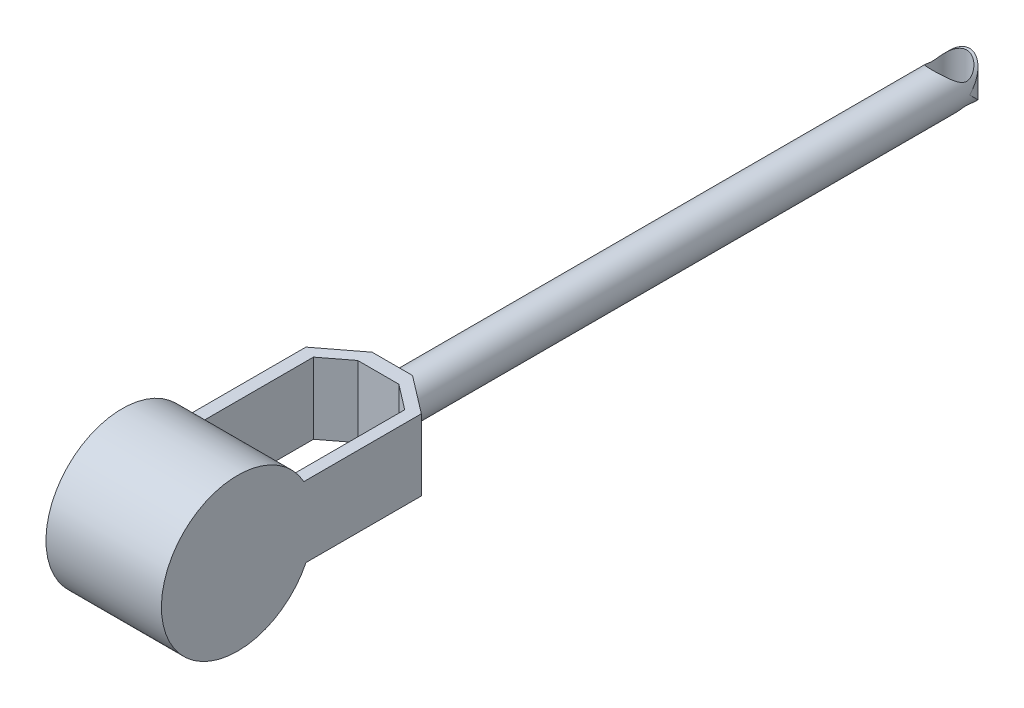
SolidWorks part; units mm, degrees
ref_plane "Front Plane" through (0, 0, 0) normal (0, 0, 1) x (1, 0, 0)
ref_plane "Top Plane" through (0, 0, 0) normal (0, 1, 0) x (1, 0, 0)
ref_plane "Right Plane" through (0, 0, 0) normal (1, 0, 0) x (0, 0, -1)
sketch "Sketch1" plane through (0, 0, 0) normal (0, 0, 1) x (1, 0, 0)
  circle A0 centre (0, 0) radius 35
  dimension "D1" = 70
extrude "Boss-Extrude1" add sketch "Sketch1" along normal blind 1000
sketch "Sketch21" plane through (0, 0, 0) normal (0, 1, 0) x (1, 0, 0)
  line L0 (35, -1000) -> (35, 0) construction
  line L1 (-35, 0) -> (-35, -1000) construction
  line L2 (-35, -35) -> (-35, -1575.0233)
  line L3 (-35, -1575.0233) -> (35, -1575.0233)
  line L4 (35, -1575.0233) -> (35, -35)
  line L5 (-30, -35) -> (-30, -1570.0233)
  line L6 (-30, -1570.0233) -> (30, -1570.0233)
  line L7 (30, -1570.0233) -> (30, -35)
  line L8 (-35, -35) -> (-35, 14.5619)
  line L9 (-35, 14.5619) -> (35, 14.5619)
  line L10 (35, 14.5619) -> (35, -35)
  arc A0 (0, 0) -> (35, -35) centre (0, -35) cw
  arc A1 (0, 0) -> (-35, -35) centre (0, -35) ccw
  arc A2 (0, -5) -> (-30, -35) centre (0, -35) ccw
  arc A3 (0, -5) -> (30, -35) centre (0, -35) cw
  dimension "D1" = 5
extrude "Cut-Extrude1" cut sketch "Sketch21" against normal mid plane 1500 contours A1 A0 L10 L9 L8
sketch "Sketch22" plane through (0, 0, 0) normal (0, 1, 0) x (1, 0, 0)
  circle A0 centre (0, -35) radius 30
extrude "Cut-Extrude2" cut sketch "Sketch22" against normal mid plane 1500
sketch "Sketch23" plane through (0, 0, 1000) normal (0, 0, 1) x (1, 0, 0)
  line L1 (-183.4481, 100.684) -> (183.4481, 100.684)
  line L2 (-183.4481, 100.684) -> (-183.4481, -100.684)
  line L3 (-183.4481, -100.684) -> (183.4481, -100.684)
  line L4 (183.4481, 100.684) -> (183.4481, -100.684)
  line L5 (-183.4481, 100.684) -> (183.4481, -100.684) construction
  line L6 (-183.4481, -100.684) -> (183.4481, 100.684) construction
  point P0 (0, 0)
extrude "Boss-Extrude2" add sketch "Sketch23" along normal blind 500
sketch "Sketch24" plane through (0, -100.684, 0) normal (0, -1, 0) x (1, 0, 0)
  line L0 (0, 1000) -> (0, 1500) construction
  line L1 (-35, 1000) -> (35, 1000) construction
  line L2 (-183.4481, 1500) -> (183.4481, 1500) construction
  line L3 (0, 1500) -> (-100, 1500) construction
  line L4 (0, 1500) -> (100, 1500) construction
  line L5 (-100, 1500) -> (-100, 1049.7732)
  line L6 (-100, 1049.7732) -> (-35, 1000)
  line L7 (-35, 1000) -> (35, 1000)
  line L8 (35, 1000) -> (100, 1049.7732)
  line L9 (100, 1049.7732) -> (100, 1500)
  line L10 (100, 1500) -> (79.5936, 1500)
  line L11 (79.5936, 1500) -> (79.5936, 1058.1624)
  line L12 (79.5936, 1058.1624) -> (36.1379, 1024.8866)
  line L13 (36.1379, 1024.8866) -> (-35, 1024.8866)
  line L14 (-35, 1024.8866) -> (-78.4557, 1058.1624)
  line L15 (-78.4557, 1058.1624) -> (-78.4557, 1500)
  line L16 (-78.4557, 1500) -> (-100, 1500)
  line L17 (-35, 1000) -> (-35, -188.3631)
  line L18 (-35, -188.3631) -> (35, -188.3631)
  line L19 (35, -188.3631) -> (35, 1000)
  line M15 (-183.4481, 1000) -> (183.4481, 1000)
  line M16 (183.4481, 1000) -> (183.4481, 1500)
  line M17 (183.4481, 1500) -> (-183.4481, 1500)
  line M18 (-183.4481, 1500) -> (-183.4481, 1000)
extrude "Cut-Extrude4" cut sketch "Sketch24" against normal blind 500 contours L15 L14 L13 L12 L11 M17 | L6 L5 M17 M18 M15 | L9 L8 M15 M16 M17
sketch "Sketch26" plane through (-100, 0, 0) normal (-1, 0, 0) x (0, 0, 1)
  line L0 (1000, 0) -> (1500, 0) construction
  line L1 (1500, 100.684) -> (1500, -100.684) construction
  line L2 (1500, 100.684) -> (1500, -100.684) construction
  line L3 (1500, 61.6664) -> (1500, 100.684)
  line L4 (1500, -100.684) -> (1500, -61.6664)
  line L5 (1500, 61.6664) -> (1000, 61.6664)
  line L6 (1000, 100.684) -> (1000, 0) construction
  line L7 (1000, 61.6664) -> (1000, 100.684)
  line L8 (1000, 100.684) -> (1024.8866, 100.684)
  line L9 (1049.7732, 100.684) -> (1000, 100.684) construction
  line L10 (1500, 100.684) -> (1000, 100.684)
  line L11 (1500, -61.6664) -> (1000, -61.6664)
  line L12 (1000, 0) -> (1000, -100.684) construction
  line L13 (1000, -61.6664) -> (1000, -100.684)
  line L14 (1000, -100.684) -> (1500, -100.684)
  line M3 (1500, 100.684) -> (1049.7732, 100.684)
  line M4 (1049.7732, 100.684) -> (1049.7732, -100.684)
  line M5 (1049.7732, -100.684) -> (1500, -100.684)
  line M6 (1500, -100.684) -> (1500, 100.684)
extrude "Cut-Extrude5" cut sketch "Sketch26" against normal blind 500 contours L5 M6 M3 M4 | L10 L8 L7 L5 M4 | L11 M6 M4 M5 | L13 L14 L11 M4
sketch "Sketch27" plane through (-100, 0, 0) normal (-1, 0, 0) x (0, 0, 1)
  line L0 (1500, 61.6664) -> (1500, -61.6664) construction
  circle A0 centre (1368, -3.4319) radius 132
  point P2 (1363.4327, -3.4319)
extrude "Boss-Extrude3" add sketch "Sketch27" against normal up to surface (200 mm away) up to face at (100, 0, 1274.8866)
sketch "Sketch28" plane through (-100, 0, 0) normal (-1, 0, 0) x (0, 0, 1)
  line L0 (1368, 128.5681) -> (1576.6741, 113.6817)
  line L1 (1576.6741, 113.6817) -> (1604.9219, -125.0794)
  line L2 (1604.9219, -125.0794) -> (1368, -201.0794)
  line L3 (1368, -135.4319) -> (1368, -201.0794)
  arc A0 (1368, 128.5681) -> (1368, -135.4319) centre (1368, -3.4319) cw
  arc A1 (1482.8312, 61.6664) -> (1253.1688, 61.6664) centre (1368, -3.4319) ccw construction
  arc A2 (1249.5401, -61.6664) -> (1486.4599, -61.6664) centre (1368, -3.4319) ccw construction
  line M1 (1486.4599, -61.6664) -> (1500, -61.6664)
  line M2 (1500, -61.6664) -> (1500, 61.6664)
  line M3 (1500, 61.6664) -> (1482.8312, 61.6664)
  arc M4 (1482.8312, 61.6664) -> (1253.1688, 61.6664) centre (1368, -3.4319) ccw
  arc M8 (1249.5401, -61.6664) -> (1486.4599, -61.6664) centre (1368, -3.4319) ccw
extrude "Cut-Extrude8" cut sketch "Sketch28" against normal through all contours L3 L2 L1 L0 M8 M4 M3 M2 M1 | A0 M2 M1 | A0 M3 M2
